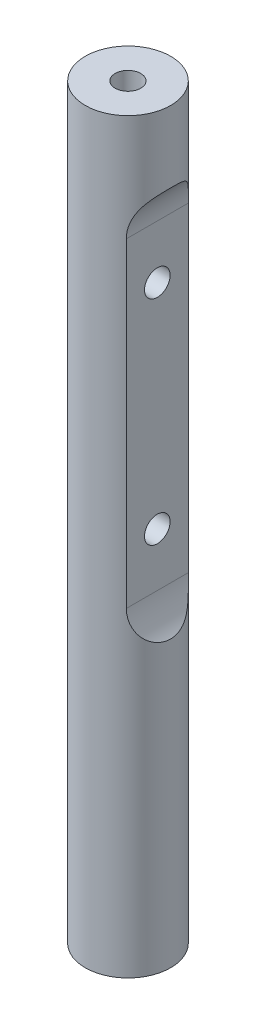
SolidWorks part; units mm, degrees
ref_plane "Front Plane" through (0, 0, 0) normal (0, 0, 1) x (1, 0, 0)
ref_plane "Top Plane" through (0, 0, 0) normal (0, 1, 0) x (1, 0, 0)
ref_plane "Right Plane" through (0, 0, 0) normal (1, 0, 0) x (0, 0, -1)
sketch "Sketch1" plane through (0, 0, 0) normal (0, 1, 0) x (1, 0, 0)
  circle A0 centre (0, 0) radius 5.08
  dimension "D1" = 10.16
extrude "Boss-Extrude1" add sketch "Sketch1" along normal blind 88.9
hole_wizard "Tapped Hole for #4-40 Helicoil1" positions "Sketch2" profile "Sketch4" tap size "#4-40" standard "Helicoil® Inch"
sketch "Sketch2" plane through (0, 88.9, 0) normal (0, 1, 0) x (1, 0, 0)
  point P0 (0, 0)
sketch "Sketch4" plane through (0, 88.9, 0) normal (1, 0, 0) x (0, 0, 1)
  line L0 (0, 0) -> (0, 9.0437)
  line L1 (0, 9.0437) -> (1.524, 8.128)
  line L2 (1.524, 8.128) -> (1.524, 0)
  line L5 (1.524, 0) -> (0, 0)
  line L10 (0, 9.0437) -> (-1.524, 8.128) construction
  line L11 (0, -6.35) -> (0, 107.95) construction
  dimension "Tap Drill Dia." = 3.048
  dimension "Tap Drill Depth" = 8.128
  dimension "Drill Angle" = 118
cosmetic thread "Hole Thread1" parameters "D1"=3.556, "D2"=3.7414
hole_wizard "Tapped Hole for #4-40 Helicoil2" positions "Sketch7" profile "Sketch6" tap size "#4-40" standard "Helicoil® Inch"
sketch "Sketch7" plane through (0, 0, 0) normal (0, -1, 0) x (-1, 0, 0)
  point P0 (0, 0)
sketch "Sketch6" plane through (0, 0, 0) normal (1, 0, 0) x (0, 0, -1)
  line L0 (0, 0) -> (0, 9.0437)
  line L1 (0, 9.0437) -> (1.524, 8.128)
  line L2 (1.524, 8.128) -> (1.524, 0)
  line L5 (1.524, 0) -> (0, 0)
  line L10 (0, 9.0437) -> (-1.524, 8.128) construction
  line L11 (0, -6.35) -> (0, 107.95) construction
  dimension "Tap Drill Dia." = 3.048
  dimension "Tap Drill Depth" = 8.128
  dimension "Drill Angle" = 118
cosmetic thread "Hole Thread2" parameters "D1"=3.556, "D2"=3.7414
sketch "Sketch8" plane through (0, 0, 0) normal (0, 0, 1) x (1, 0, 0)
  line L0 (3.4925, 76.2) -> (3.4925, 38.1)
  line L1 (-5.08, 0) -> (5.08, 0) construction
  line L2 (5.08, 0) -> (5.08, 88.9) construction
  line L3 (5.08, 33.8999) -> (5.08, 88.9)
  arc A0 (5.08, 80.4001) -> (3.4925, 76.2) centre (9.8425, 76.2) ccw
  arc A1 (3.4925, 38.1) -> (5.08, 33.8999) centre (9.8425, 38.1) ccw
  dimension "D4" = 12.7
  dimension "D5" = 12.7
  dimension "D1" = 38.1
  dimension "D2" = 38.1
  dimension "D3" = 1.5875
extrude "Cut-Extrude1" cut sketch "Sketch8" along normal through all both and the other way through all contours L0 A1 L3 A0
sketch "Sketch9" plane through (3.4925, 0, 0) normal (1, 0, 0) x (0, 0, -1)
  line L0 (0, 76.2) -> (0, 38.1) construction
  line L1 (-3.689, 76.2) -> (3.689, 76.2) construction
  line L2 (-3.689, 38.1) -> (3.689, 38.1) construction
  line L3 (-3.689, 69.85) -> (3.689, 69.85) construction
  line L4 (-3.689, 76.2) -> (-3.689, 38.1) construction
  line L5 (3.689, 38.1) -> (3.689, 76.2) construction
  line L6 (-3.689, 44.45) -> (3.689, 44.45) construction
  dimension "D1" = 6.35
  dimension "D2" = 6.35
hole_wizard "Tapped Hole for #4-40 Helicoil3" positions "Sketch10" profile "Sketch11" tap size "#4-40" standard "Helicoil® Inch" end condition through all
sketch "Sketch10" plane through (3.4925, 0, 0) normal (1, 0, 0) x (0, 0, -1)
  point P0 (0, 69.85)
  point P2 (0, 44.45)
sketch "Sketch11" plane through (3.4925, 69.85, 0) normal (0, 1, 0) x (0, 0, -1)
  line L0 (0, 0) -> (0, 8.5725)
  line L1 (0, 8.5725) -> (1.524, 8.5725)
  line L2 (1.524, 8.5725) -> (1.524, 0)
  line L5 (1.524, 0) -> (0, 0)
  line L11 (0, -6.35) -> (0, 107.95) construction
  dimension "Thru Tap Drill Dia." = 3.048
  dimension "Thru Tap Drill Depth" = 8.5725
cosmetic thread "Hole Thread3" parameters "D1"=3.556, "D2"=3.7414
cosmetic thread "Hole Thread4" parameters "D1"=3.556, "D2"=3.7414
